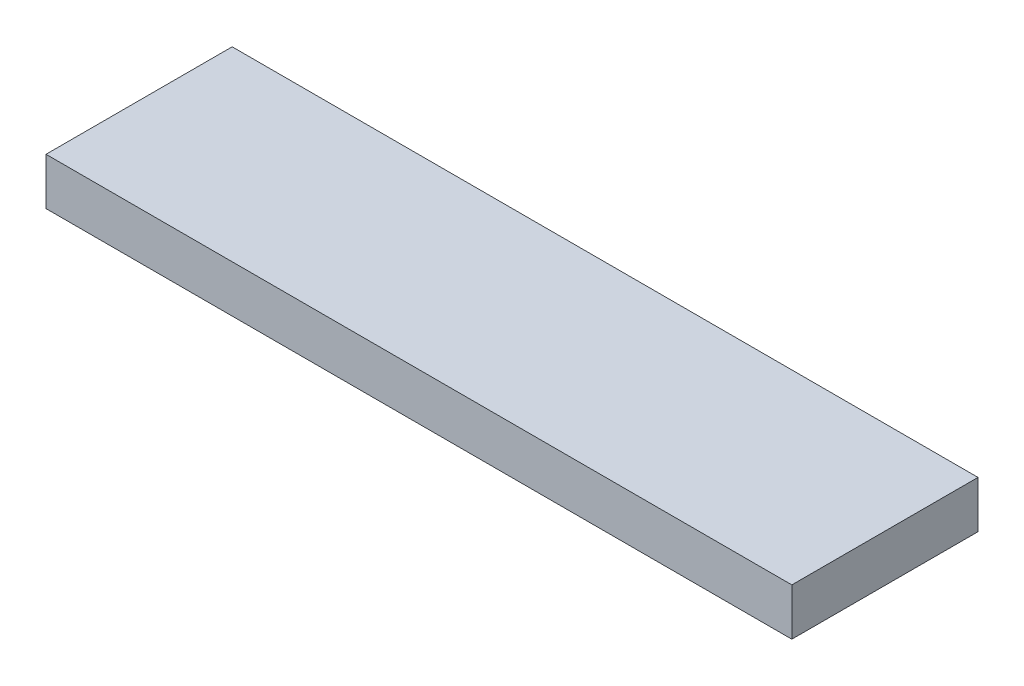
SolidWorks part; units mm, degrees
ref_plane "Front Plane" through (0, 0, 0) normal (0, 0, 1) x (1, 0, 0)
ref_plane "Top Plane" through (0, 0, 0) normal (0, 1, 0) x (1, 0, 0)
ref_plane "Right Plane" through (0, 0, 0) normal (1, 0, 0) x (0, 0, -1)
sketch "Sketch1" plane through (0, 0, 0) normal (0, 1, 0) x (1, 0, 0)
  line L1 (-79.2458, -19.7801) -> (79.2458, -19.7801)
  line L2 (-79.2458, -19.7801) -> (-79.2458, 19.7801)
  line L3 (-79.2458, 19.7801) -> (79.2458, 19.7801)
  line L4 (79.2458, -19.7801) -> (79.2458, 19.7801)
  line L5 (-79.2458, -19.7801) -> (79.2458, 19.7801) construction
  line L6 (-79.2458, 19.7801) -> (79.2458, -19.7801) construction
  point P0 (0, 0)
extrude "Boss-Extrude1" add sketch "Sketch1" along normal blind 10
